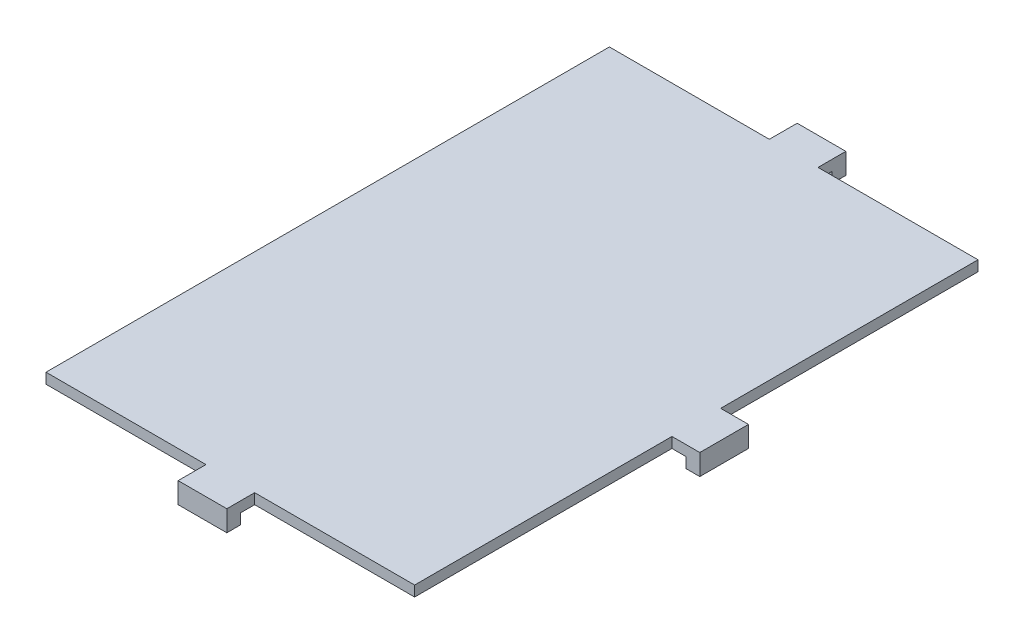
SolidWorks part; units mm, degrees
ref_plane "Front Plane" through (0, 0, 0) normal (0, 0, 1) x (1, 0, 0)
ref_plane "Top Plane" through (0, 0, 0) normal (0, 1, 0) x (1, 0, 0)
ref_plane "Right Plane" through (0, 0, 0) normal (1, 0, 0) x (0, 0, -1)
sketch "Sketch1" plane through (0, 0, 0) normal (0, 1, 0) x (1, 0, 0)
  line L0 (30, 81) -> (53, 81)
  line L1 (0, 0) -> (23, 0)
  line L2 (0, 0) -> (0, 81)
  line L3 (0, 81) -> (23, 81)
  line L4 (53, 0) -> (53, 37)
  line L6 (23, 0) -> (23, -2)
  line L7 (23, -2) -> (30, -2)
  line L8 (30, 0) -> (30, -2)
  line L11 (23, 83) -> (30, 83)
  line L12 (23, 83) -> (23, 81)
  line L14 (30, 83) -> (30, 81)
  line L15 (53, 44) -> (53, 81)
  line L16 (30, 0) -> (53, 0)
  line L17 (53, 44) -> (55, 44)
  line L19 (53, 37) -> (55, 37)
  line L20 (55, 44) -> (55, 37)
  point P5 (26.5, 0)
  point P10 (26.5, 81)
  point P15 (53, 40.5)
  dimension "D1" = 81
  dimension "D2" = 53
  dimension "D3" = 2
  dimension "D4" = 7
  dimension "D5" = 7
  dimension "D6" = 2
  dimension "D7" = 7
  dimension "D8" = 2
extrude "Boss-Extrude1" add sketch "Sketch1" along normal blind 1.5
sketch "Sketch2" plane through (0, 1.5, 0) normal (0, 1, 0) x (1, 0, 0)
  line L2 (23, 83) -> (30, 83)
  line L3 (23, 83) -> (23, 85)
  line L4 (23, 85) -> (30, 85)
  line L5 (30, 83) -> (30, 85)
  line L6 (55, 44) -> (57, 44)
  line L7 (55, 44) -> (55, 37)
  line L8 (55, 37) -> (57, 37)
  line L9 (57, 44) -> (57, 37)
  line L10 (23, -2) -> (30, -2)
  line L11 (23, -2) -> (23, -4)
  line L12 (23, -4) -> (30, -4)
  line L13 (30, -2) -> (30, -4)
  dimension "D1" = 7
  dimension "D2" = 7
  dimension "D3" = 7
  dimension "D4" = 2
  dimension "D5" = 2
  dimension "D6" = 2
extrude "Boss-Extrude2" add sketch "Sketch2" against normal blind 3
